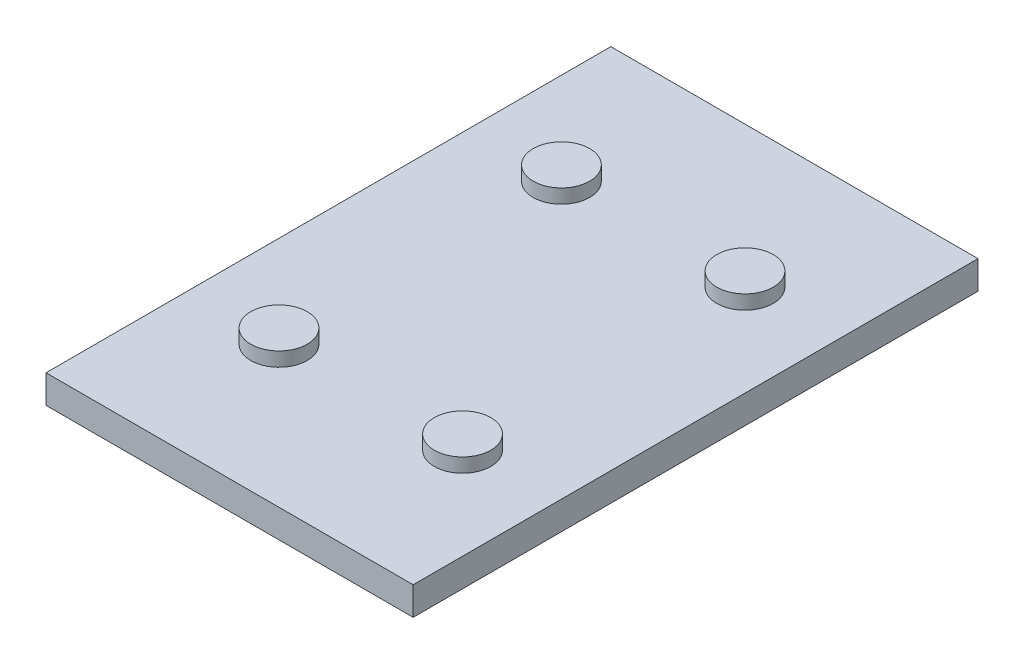
SolidWorks part; units mm, degrees
ref_plane "Front Plane" through (0, 0, 0) normal (0, 0, 1) x (1, 0, 0)
ref_plane "Top Plane" through (0, 0, 0) normal (0, 1, 0) x (1, 0, 0)
ref_plane "Right Plane" through (0, 0, 0) normal (1, 0, 0) x (0, 0, -1)
sketch "Sketch1" plane through (0, 0, 0) normal (0, 1, 0) x (1, 0, 0)
  line L1 (-106.569, 229.7043) -> (223.631, 229.7043)
  line L2 (-106.569, 229.7043) -> (-106.569, -278.2957)
  line L3 (-106.569, -278.2957) -> (223.631, -278.2957)
  line L4 (223.631, 229.7043) -> (223.631, -278.2957)
  dimension "D1" = 508
  dimension "D2" = 330.2
extrude "Boss-Extrude1" add sketch "Sketch1" along normal blind 25.4
sketch "Sketch2" plane through (0, 25.4, 0) normal (0, 1, 0) x (1, 0, 0)
  line L2 (223.631, 229.7043) -> (-106.569, 229.7043) construction
  line L3 (223.631, -278.2957) -> (223.631, 229.7043) construction
  circle A0 centre (-24.019, 102.7043) radius 25.4
  circle A1 centre (141.081, 102.7043) radius 25.4
  circle A2 centre (141.081, -151.2957) radius 25.4
  circle A3 centre (-24.019, -151.2957) radius 25.4
  point P12 (58.531, -24.2957)
  dimension "D1" = 50.8
  dimension "D4" = 254
  dimension "D5" = 165.1
  dimension "D6" = 82.55
  dimension "D7" = 127
  dimension "D2" = 2
  dimension "D3" = 2
extrude "Boss-Extrude2" add sketch "Sketch2" along normal blind 12.7
